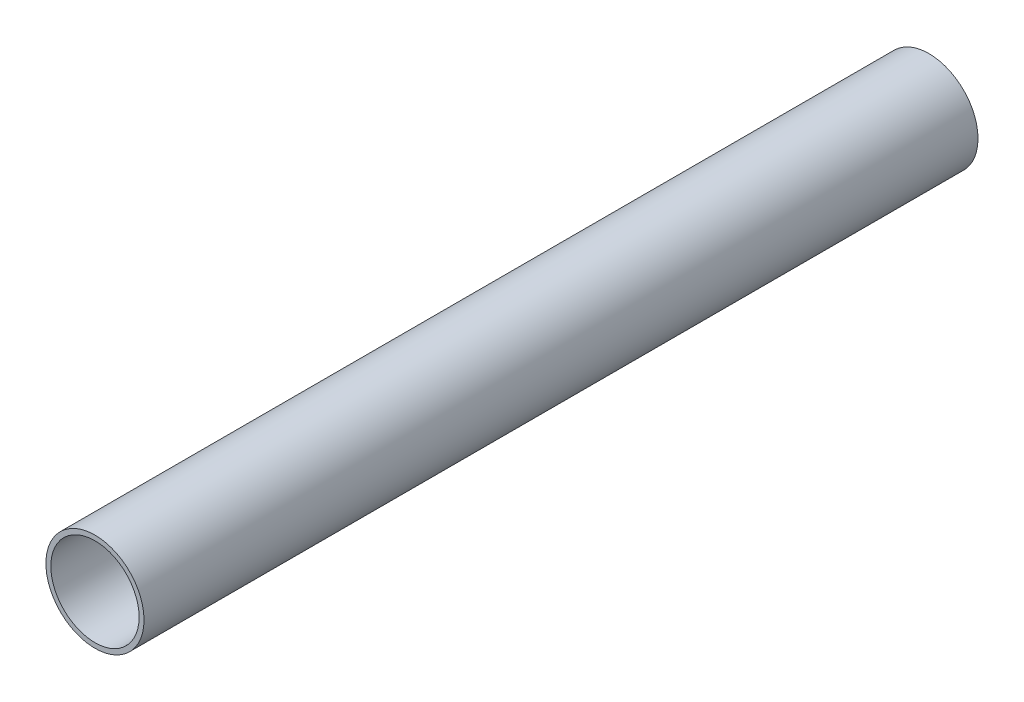
SolidWorks part; units mm, degrees
material "Carbon Fiber Tube - UD Approx"
ref_plane "Front Plane" through (0, 0, 0) normal (0, 0, 1) x (1, 0, 0)
ref_plane "Top Plane" through (0, 0, 0) normal (0, 1, 0) x (1, 0, 0)
ref_plane "Right Plane" through (0, 0, 0) normal (1, 0, 0) x (0, 0, -1)
sketch "Sketch1" plane through (0, 0, 0) normal (0, 0, 1) x (1, 0, 0)
  circle A0 centre (0, 0) radius 10
  circle A1 centre (0, 0) radius 9
  dimension "D1" = 20
  dimension "D2" = 18
extrude "Boss-Extrude1" add sketch "Sketch1" along normal blind 170
